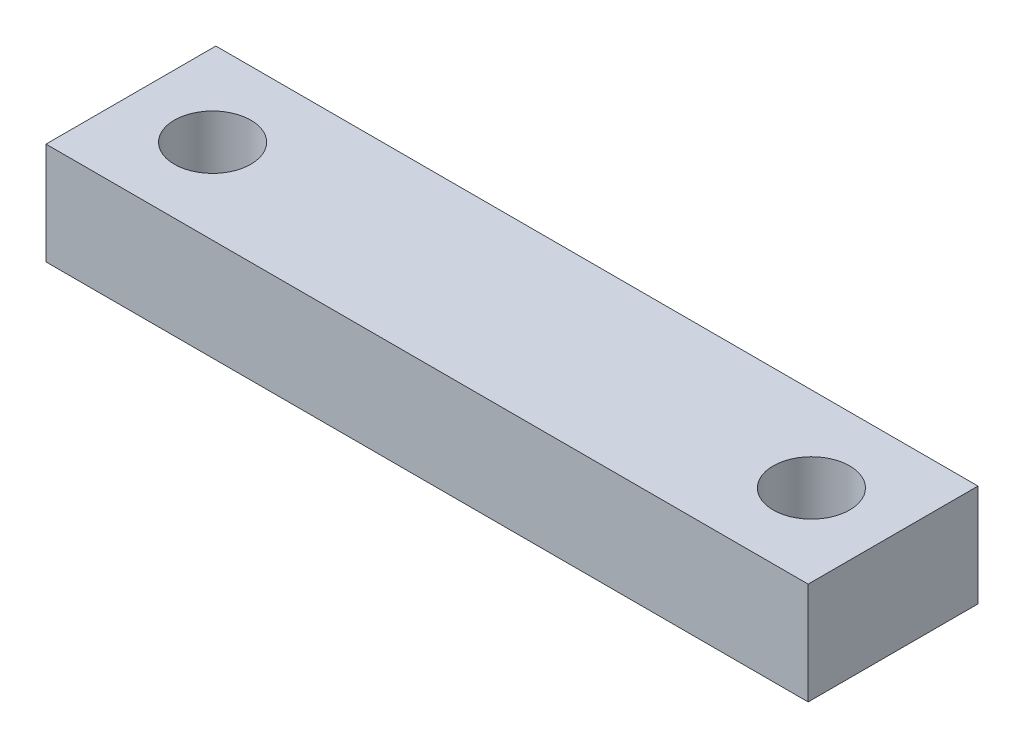
SolidWorks part; units mm, degrees
ref_plane "Front Plane" through (0, 0, 0) normal (0, 0, 1) x (1, 0, 0)
ref_plane "Top Plane" through (0, 0, 0) normal (0, 1, 0) x (1, 0, 0)
ref_plane "Right Plane" through (0, 0, 0) normal (1, 0, 0) x (0, 0, -1)
sketch "Sketch1" plane through (0, 0, 0) normal (0, 1, 0) x (1, 0, 0)
  line L1 (-35.56, -7.9248) -> (35.56, -7.9248)
  line L2 (-35.56, -7.9248) -> (-35.56, 7.9248)
  line L3 (-35.56, 7.9248) -> (35.56, 7.9248)
  line L4 (35.56, -7.9248) -> (35.56, 7.9248)
  line L5 (-35.56, -7.9248) -> (35.56, 7.9248) construction
  line L6 (-35.56, 7.9248) -> (35.56, -7.9248) construction
  point P0 (0, 0)
  dimension "D1" = 71.12
  dimension "D2" = 15.8496
extrude "Boss-Extrude1" add sketch "Sketch1" along normal blind 9.525
hole_wizard "K (0.281) Diameter Hole1" positions "Sketch2" profile "Sketch3" hole size "K" standard "ANSI Inch" end condition up to next
sketch "Sketch2" plane through (0, 9.525, 0) normal (0, 1, 0) x (1, 0, 0)
  line L0 (-27.94, 0) -> (27.94, 0) construction
  point P0 (-27.94, 0)
  point P2 (27.94, 0)
  point P8 (0, 0)
  dimension "D1" = 55.88
sketch "Sketch3" plane through (-27.94, 9.525, 0) normal (1, 0, 0) x (0, 0, 1)
  line L0 (0, 0) -> (0, 9.525)
  line L1 (0, 9.525) -> (3.5687, 9.525)
  line L2 (3.5687, 9.525) -> (3.5687, 0)
  line L5 (3.5687, 0) -> (0, 0)
  line L11 (0, -6.35) -> (0, 107.95) construction
  dimension "Thru Hole Dia." = 7.1374
  dimension "Thru Hole Depth" = 9.525
